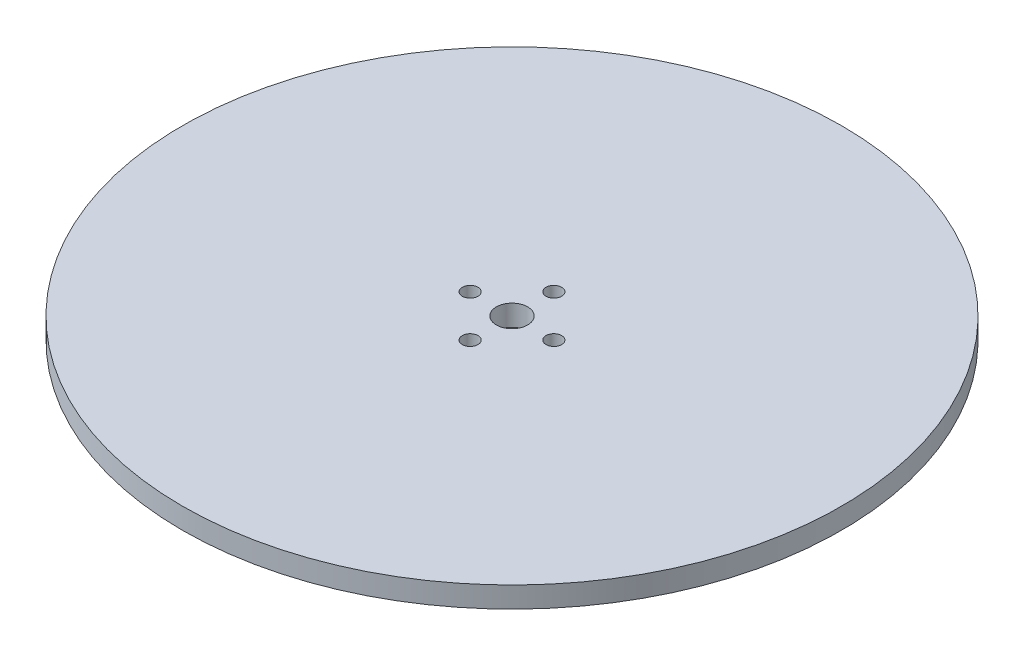
SolidWorks part; units mm, degrees
ref_plane "前视基准面" through (0, 0, 0) normal (0, 0, 1) x (1, 0, 0)
ref_plane "上视基准面" through (0, 0, 0) normal (0, 1, 0) x (1, 0, 0)
ref_plane "右视基准面" through (0, 0, 0) normal (1, 0, 0) x (0, 0, -1)
sketch "草图1" plane through (0, 0, 0) normal (0, 1, 0) x (1, 0, 0)
  circle A0 centre (0, 0) radius 63
  dimension "D1" = 126
extrude "凸台-拉伸1" add sketch "草图1" along normal blind 4
sketch "草图2" plane through (0, 4, 0) normal (0, 1, 0) x (1, 0, 0)
  circle A0 centre (8, 0) radius 1.5
  circle A1 centre (0, 8) radius 1.5
  circle A2 centre (-8, 0) radius 1.5
  circle A3 centre (0, -8) radius 1.5
  circle A4 centre (0, 0) radius 3
  dimension "D1" = 3
  dimension "D2" = 3
  dimension "D3" = 3
  dimension "D4" = 3
  dimension "D5" = 16
  dimension "D6" = 8
  dimension "D7" = 8
  dimension "D8" = 16
  dimension "D9" = 6
  dimension "D10" = 8
  dimension "D11" = 8
  dimension "D12" = 8
  dimension "D13" = 8
extrude "切除-拉伸1" cut sketch "草图2" against normal through all
